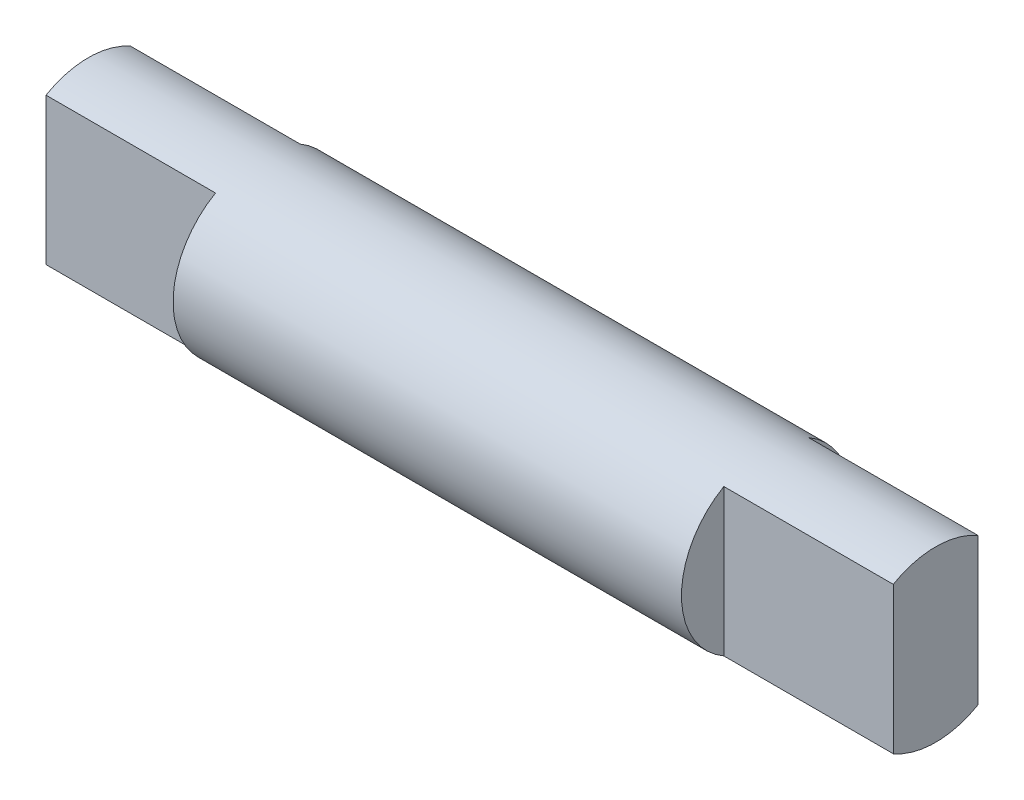
SolidWorks part; units mm, degrees
ref_plane "Front Plane" through (0, 0, 0) normal (0, 0, 1) x (1, 0, 0)
ref_plane "Top Plane" through (0, 0, 0) normal (0, 1, 0) x (1, 0, 0)
ref_plane "Right Plane" through (0, 0, 0) normal (1, 0, 0) x (0, 0, -1)
sketch "Sketch1" plane through (0, 0, 0) normal (1, 0, 0) x (0, 0, -1)
  circle A0 centre (0, 0) radius 5
  dimension "D1" = 10
extrude "Boss-Extrude1" add sketch "Sketch1" along normal blind 5 and the other way blind 45
sketch "Sketch2" plane through (0, 0, 0) normal (0, 1, 0) x (1, 0, 0)
  line L0 (-45, 5) -> (-45, -5) construction
  line L1 (-45, -2.5) -> (-35, -2.5)
  line L3 (-45, 2.5) -> (-35, 2.5)
  line L5 (-45, -2.5) -> (-45, -5)
  line L6 (-45, -5) -> (-35, -5)
  line L7 (-45, -5) -> (5, -5) construction
  line L8 (-35, -5) -> (-35, -2.5)
  line L9 (-45, 2.5) -> (-45, 5)
  line L10 (-45, 5) -> (-35, 5)
  line L11 (5, 5) -> (-45, 5) construction
  line L12 (-35, 5) -> (-35, 2.5)
  line L14 (5, -5) -> (-5, -5)
  line L15 (5, -5) -> (5, -2.5)
  line L16 (5, -2.5) -> (-5, -2.5)
  line L17 (-5, -5) -> (-5, -2.5)
  line L18 (5, 5) -> (-5, 5)
  line L19 (5, 5) -> (5, 2.5)
  line L20 (5, 2.5) -> (-5, 2.5)
  line L21 (-5, 5) -> (-5, 2.5)
  dimension "D1" = 5
  dimension "D2" = 10
extrude "Cut-Extrude1" cut sketch "Sketch2" against normal through all both and the other way through all
